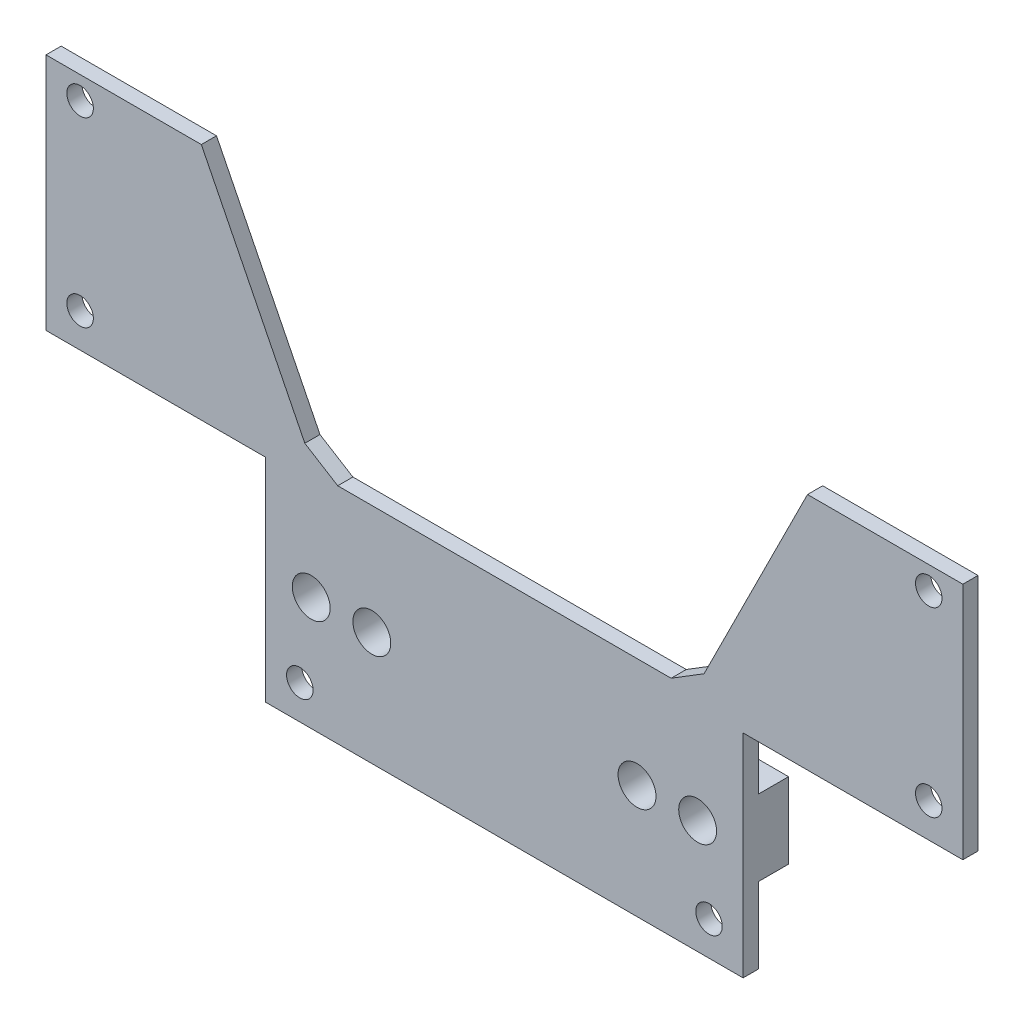
SolidWorks part; units mm, degrees
material "uhlíková ocel 7850"
ref_plane "Přední rovina" through (0, 0, 0) normal (0, 0, 1) x (1, 0, 0)
ref_plane "Horní rovina" through (0, 0, 0) normal (0, 1, 0) x (1, 0, 0)
ref_plane "Pravá rovina" through (0, 0, 0) normal (1, 0, 0) x (0, 0, -1)
sketch "Skica1" plane through (0, 0, 0) normal (0, 0, 1) x (1, 0, 0)
  line L0 (0, 0) -> (0, 68.9305) construction
  line L1 (-31.5, 0) -> (31.5, 0)
  line L2 (31.5, 0) -> (31.5, 28)
  line L3 (31.5, 28) -> (60.5, 28)
  line L4 (60.5, 28) -> (60.5, 59.5)
  line L5 (60.5, 59.5) -> (-60.5, 59.5)
  line L6 (-60.5, 28) -> (-60.5, 59.5)
  line L7 (-31.5, 28) -> (-60.5, 28)
  line L8 (-31.5, 0) -> (-31.5, 28)
  point P9 (0, 59.5)
  dimension "D1" = 31.5
  dimension "D2" = 28
  dimension "D3" = 29
  dimension "D4" = 31.5
extrude "Přidat vysunutím1" add sketch "Skica1" along normal blind 2
sketch "Skica2" plane through (0, 0, 0) normal (0, 0, -1) x (-1, 0, 0)
  circle A0 centre (-56, 56.5) radius 1.75
  circle A1 centre (-56, 32.5) radius 1.75
  circle A2 centre (-27, 4.5) radius 1.75
  circle A3 centre (27, 4.5) radius 1.75
  circle A4 centre (56, 32.5) radius 1.75
  circle A5 centre (56, 56.5) radius 1.75
  dimension "D1" = 3.5
extrude "Odebrat vysunutím1" cut sketch "Skica2" against normal blind 10
sketch "Skica3" plane through (0, 0, 0) normal (0, 0, 1) x (1, 0, 0)
  line L0 (-31.5, 28) -> (-31.5, 0) construction
  line L1 (-31.5, 20) -> (31.5, 20)
  line L2 (-31.5, 20) -> (-31.5, 10)
  line L3 (-31.5, 10) -> (31.5, 10)
  line L4 (31.5, 20) -> (31.5, 10)
  line L5 (31.5, 0) -> (31.5, 28) construction
  line L6 (-31.5, 0) -> (31.5, 0) construction
  dimension "D1" = 10
  dimension "D2" = 10
extrude "Přidat vysunutím2" add sketch "Skica3" against normal blind 4
sketch "Skica4" plane through (0, 0, -4) normal (0, 0, -1) x (-1, 0, 0)
  line L0 (31.5, 15) -> (0, 15) construction
  line L1 (31.5, 20) -> (31.5, 10) construction
  line L2 (0, 15) -> (0, 0) construction
  circle A0 centre (17.5, 15) radius 2.5
  circle A1 centre (25.5, 15) radius 2.5
  circle A2 centre (-25.5, 15) radius 2.5
  circle A3 centre (-17.5, 15) radius 2.5
  dimension "D1" = 5
  dimension "D2" = 8
  dimension "D3" = 14
extrude "Odebrat vysunutím2" cut sketch "Skica4" against normal blind 24
sketch "Skica5" plane through (0, 0, 2) normal (0, 0, 1) x (1, 0, 0)
  line L0 (60.5, 59.5) -> (-60.5, 59.5) construction
  line L1 (40, 59.5) -> (-40, 59.5)
  line L2 (40, 59.5) -> (25, 29.5)
  line L3 (25, 29.5) -> (-25, 29.5)
  line L4 (-40, 59.5) -> (-25, 29.5)
  line L5 (0, 0) -> (0, 59.5) construction
  line L6 (-31.5, 0) -> (31.5, 0) construction
  point P10 (0, 29.5)
  dimension "D1" = 50
  dimension "D2" = 30
  dimension "D3" = 80
extrude "Odebrat vysunutím3" cut sketch "Skica5" against normal blind 10
sketch "Skica6" plane through (0, 0, 0) normal (0, 0, -1) x (-1, 0, 0)
  line L0 (-25, 29.5) -> (-26.3416, 32.1833)
  line L1 (-40, 59.5) -> (-25, 29.5) construction
  line L2 (-26.3416, 32.1833) -> (-22, 29.5)
  line L3 (-25, 29.5) -> (25, 29.5) construction
  line L4 (-22, 29.5) -> (-25, 29.5)
  line L5 (25, 29.5) -> (26.3416, 32.1833)
  line L6 (25, 29.5) -> (40, 59.5) construction
  line L7 (26.3416, 32.1833) -> (22, 29.5)
  line L8 (22, 29.5) -> (25, 29.5)
  dimension "D1" = 3
extrude "Přidat vysunutím3" add sketch "Skica6" against normal up to surface (2 mm away) up to face at (15, 15, 2)
sketch "Skica7" [suppressed] plane through (0, 0, 0) normal (0, 0, -1) x (-1, 0, 0)
  line L0 (-21.1745, 40.85) -> (-26.7745, 37.7) construction
  line L1 (-17.2245, 33.025) -> (-30.7245, 33.025)
  line L2 (-17.2245, 33.025) -> (-17.2245, 45.525)
  line L3 (-17.2245, 45.525) -> (-30.7245, 45.525)
  line L4 (-30.7245, 33.025) -> (-30.7245, 45.525)
  line L5 (-17.2245, 33.025) -> (-30.7245, 45.525) construction
  line L6 (-17.2245, 45.525) -> (-30.7245, 33.025) construction
  point P0 (-23.9745, 39.275)
  dimension "D1" = 13.5
  dimension "D2" = 12.5
extrude "Odebrat vysunutím4" [suppressed] cut sketch "Skica7" against normal blind 5
